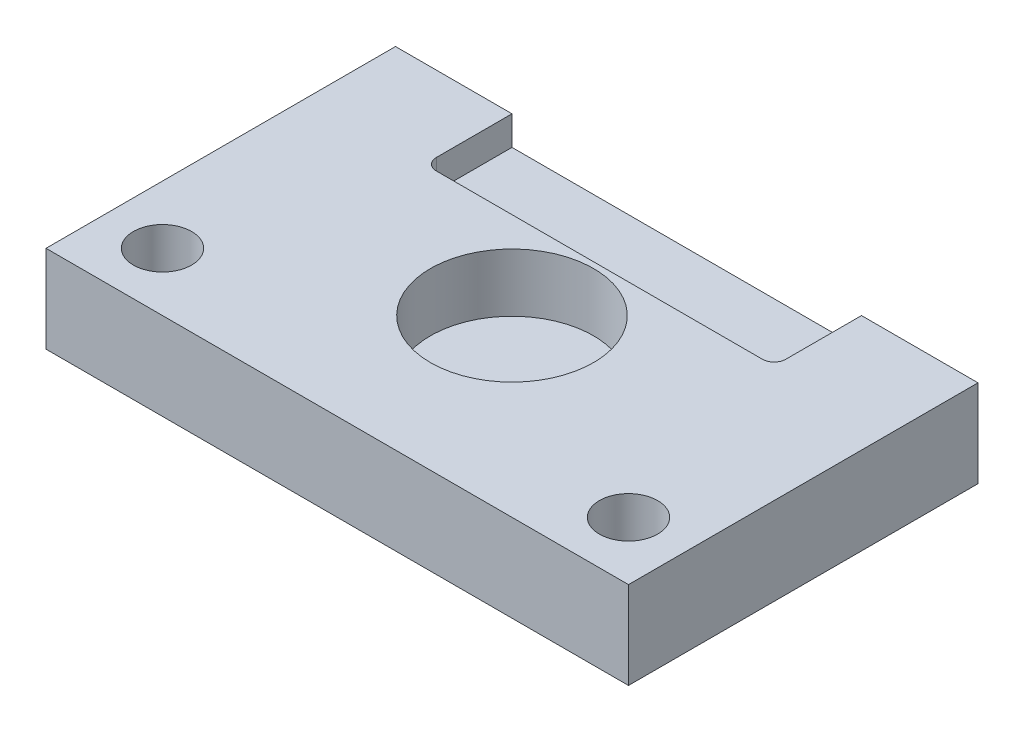
SolidWorks part; units mm, degrees
ref_plane "Ön Düzlem" through (0, 0, 0) normal (0, 0, 1) x (1, 0, 0)
ref_plane "Üst Düzlem" through (0, 0, 0) normal (0, 1, 0) x (1, 0, 0)
ref_plane "Sağ Düzlem" through (0, 0, 0) normal (1, 0, 0) x (0, 0, -1)
sketch "Çizim1" plane through (0, 0, 0) normal (0, 1, 0) x (1, 0, 0)
  line L1 (-50, -30) -> (50, -30)
  line L2 (-50, -30) -> (-50, 30)
  line L3 (-50, 30) -> (50, 30)
  line L4 (50, -30) -> (50, 30)
  line L5 (-50, -30) -> (50, 30) construction
  line L6 (-50, 30) -> (50, -30) construction
  point P0 (0, 0)
  dimension "D1" = 100
  dimension "D2" = 60
extrude "Yükseklik-Ekstrüzyon1" add sketch "Çizim1" along normal blind 15
sketch "Çizim2" plane through (0, 15, 0) normal (0, 1, 0) x (1, 0, 0)
  line L0 (0, 0) -> (0, 30) construction
  line L1 (50, 30) -> (-50, 30) construction
  line L3 (-30, 15) -> (30, 15)
  line L4 (-30, 15) -> (-30, 30)
  line L5 (-30, 30) -> (30, 30)
  line L6 (30, 15) -> (30, 30)
  line L7 (-30, 15) -> (30, 30) construction
  line L8 (-30, 30) -> (30, 15) construction
  point P5 (0, 22.5)
  dimension "D1" = 60
  dimension "D2" = 15
extrude "Kes-Ekstrüzyon1" cut sketch "Çizim2" against normal blind 5
sketch "Çizim3" plane through (0, 15, 0) normal (0, 1, 0) x (1, 0, 0)
  circle A0 centre (0, 0) radius 14
  dimension "D1" = 28
extrude "Kes-Ekstrüzyon2" cut sketch "Çizim3" against normal blind 10
sketch "Çizim4" plane through (0, 15, 0) normal (0, 1, 0) x (1, 0, 0)
  line L0 (0, 0) -> (0, 14) construction
  line L1 (-50, -20) -> (-40, -20) construction
  line L2 (-50, 30) -> (-50, -30) construction
  line L3 (-40, -20) -> (-40, -30) construction
  line L4 (-50, -30) -> (50, -30) construction
  circle A0 centre (0, 0) radius 14 construction
  circle A1 centre (-40, -20) radius 5
  circle A2 centre (40, -20) radius 5
  dimension "D3" = 10
  dimension "D1" = 10
  dimension "D2" = 10
extrude "Kes-Ekstrüzyon3" cut sketch "Çizim4" against normal through all
fillet "Radyus1" radius 2 2 edges at (-30, 12.5, -15) (30, 12.5, -15)
